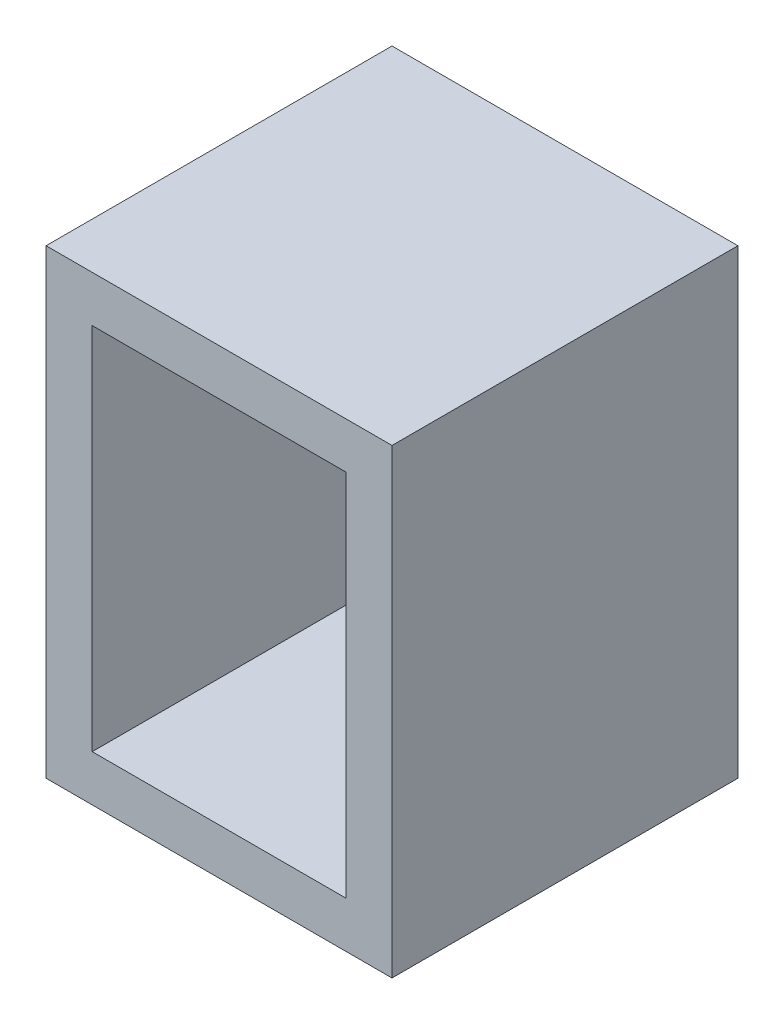
SolidWorks part; units mm, degrees
ref_plane "前视基准面" through (0, 0, 0) normal (0, 0, 1) x (1, 0, 0)
ref_plane "上视基准面" through (0, 0, 0) normal (0, 1, 0) x (1, 0, 0)
ref_plane "右视基准面" through (0, 0, 0) normal (1, 0, 0) x (0, 0, -1)
sketch "草图1" plane through (0, 0, 0) normal (0, 1, 0) x (1, 0, 0)
  line L1 (-75, 75) -> (75, 75)
  line L2 (-75, 75) -> (-75, -75)
  line L3 (-75, -75) -> (75, -75)
  line L4 (75, 75) -> (75, -75)
  line L5 (-75, 75) -> (75, -75) construction
  line L6 (-75, -75) -> (75, 75) construction
  point P0 (0, 0)
  dimension "D1" = 150
  dimension "D2" = 150
extrude "凸台-拉伸1" add sketch "草图1" along normal blind 200
shell "抽壳1" thickness 20
